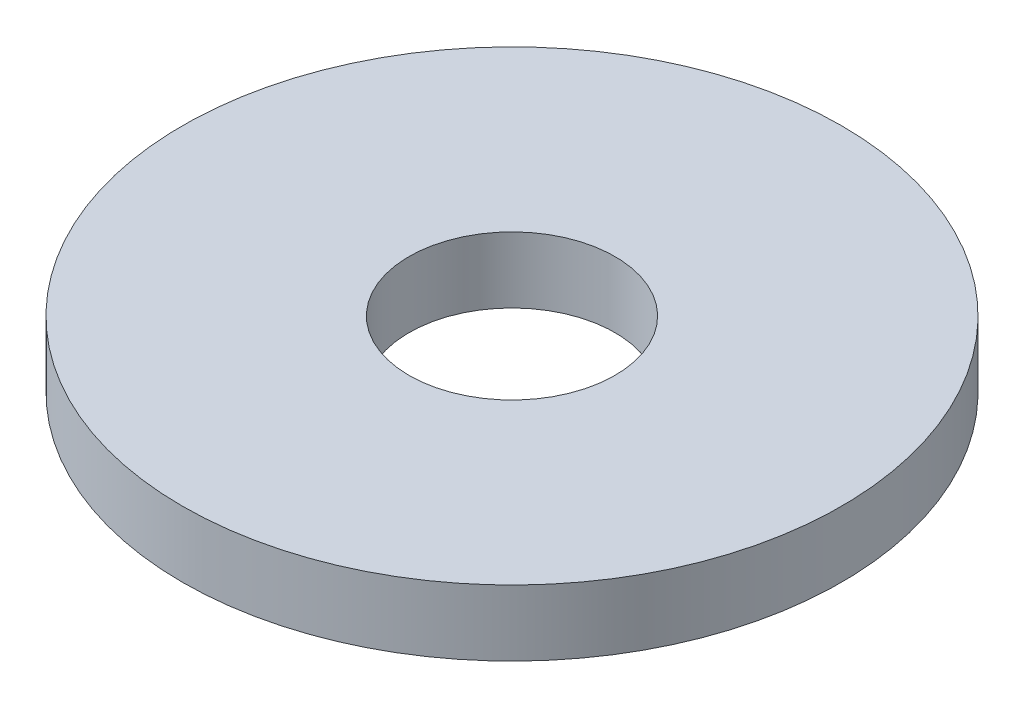
SolidWorks part; units mm, degrees
material "AISI 304"
ref_plane "Front Plane" through (0, 0, 0) normal (0, 0, 1) x (1, 0, 0)
ref_plane "Top Plane" through (0, 0, 0) normal (0, 1, 0) x (1, 0, 0)
ref_plane "Right Plane" through (0, 0, 0) normal (1, 0, 0) x (0, 0, -1)
sketch "Sketch1" plane through (0, 0, 0) normal (0, 1, 0) x (1, 0, 0)
  circle A0 centre (0, 0) radius 15.875
  circle A1 centre (0, 0) radius 4.9609
  dimension "D1" = 9.9219
  dimension "D2" = 31.75
extrude "Extrude1" add sketch "Sketch1" along normal mid plane 3.175
